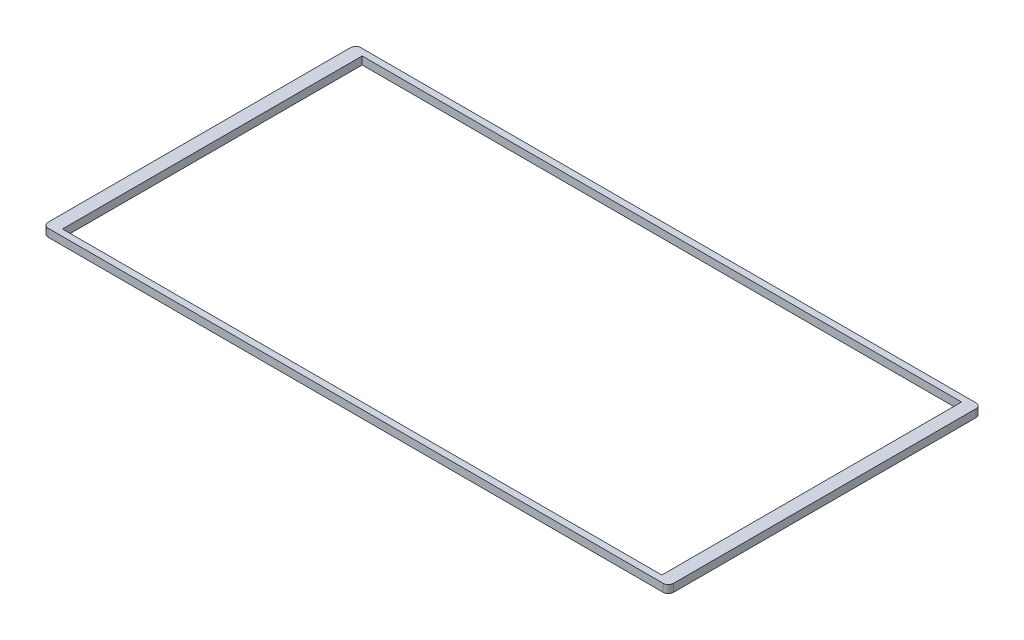
SolidWorks part; units mm, degrees
material "1023 Carbon Steel Sheet (SS)"
ref_plane "Front Plane" through (0, 0, 0) normal (0, 0, 1) x (1, 0, 0)
ref_plane "Top Plane" through (0, 0, 0) normal (0, 1, 0) x (1, 0, 0)
ref_plane "Right Plane" through (0, 0, 0) normal (1, 0, 0) x (0, 0, -1)
sketch "Sketch1" plane through (0, 0, 0) normal (0, 1, 0) x (1, 0, 0)
  line L0 (-238, 859) -> (-202, 811) construction
  line L1 (-1200, -600) -> (1200, -600)
  line L2 (-1200, -600) -> (-1200, 600)
  line L3 (-1200, 600) -> (1200, 600)
  line L4 (1200, -600) -> (1200, 600)
  line L5 (-1200, -600) -> (1200, 600) construction
  line L6 (-1200, 600) -> (1200, -600) construction
  line L7 (-830, -325) -> (-770, -325) construction
  line L8 (-830, -325) -> (-830, 325) construction
  line L9 (-830, 325) -> (-770, 325) construction
  line L10 (-770, -325) -> (-770, 325) construction
  line L11 (-830, -325) -> (-770, 325) construction
  line L12 (-830, 325) -> (-770, -325) construction
  line L13 (-202, 811) -> (-722, 421) construction
  line L14 (-238, 859) -> (-758, 469) construction
  line L15 (-758, 469) -> (-722, 421) construction
  line L16 (-758, -469) -> (-722, -421) construction
  line L17 (-758, -469) -> (-238, -859) construction
  line L18 (544.4, -705.8) -> (527.6, -648.2) construction
  line L19 (544.4, -705.8) -> (-79.6, -887.8) construction
  line L20 (527.6, -648.2) -> (-96.4, -830.2) construction
  line L21 (-79.6, -887.8) -> (-96.4, -830.2) construction
  line L22 (-238, -859) -> (-202, -811) construction
  line L23 (-722, -421) -> (-202, -811) construction
  line L25 (-1150, -575) -> (1150, -575)
  line L26 (-1150, -575) -> (-1150, 575)
  line L27 (-1150, 575) -> (1150, 575)
  line L28 (1150, -575) -> (1150, 575)
  line L29 (-1150, -575) -> (1150, 575) construction
  line L30 (-1150, 575) -> (1150, -575) construction
  circle A0 centre (0, 0) radius 500 construction
  point P7 (-800, 0)
  dimension "D1" = 1000
  dimension "D4" = 650
  dimension "D2" = 2400
  dimension "D3" = 1200
  dimension "D5" = 60
  dimension "D6" = 800
  dimension "D7" = 50
extrude "Boss-Extrude1" add sketch "Sketch1" along normal mid plane 30
fillet "Fillet1" radius 20 4 edges at (-1200, 0, -600) (1200, 0, -600) (1200, 0, 600) (-1200, 0, 600)
